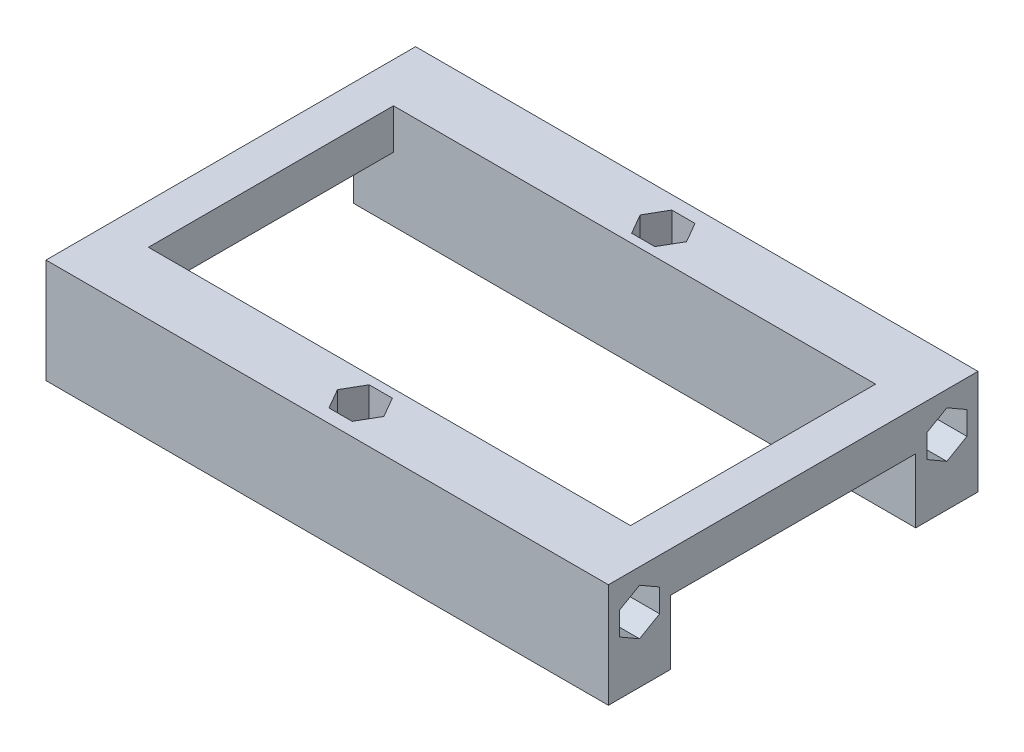
SolidWorks part; units mm, degrees
ref_plane "Front Plane" through (0, 0, 0) normal (0, 0, 1) x (1, 0, 0)
ref_plane "Top Plane" through (0, 0, 0) normal (0, 1, 0) x (1, 0, 0)
ref_plane "Right Plane" through (0, 0, 0) normal (1, 0, 0) x (0, 0, -1)
sketch "Sketch1" plane through (0, 0, 0) normal (0, 1, 0) x (1, 0, 0)
  line L1 (-35, -23) -> (35, -23)
  line L2 (-35, -23) -> (-35, 23)
  line L3 (-35, 23) -> (35, 23)
  line L4 (35, -23) -> (35, 23)
  line L5 (-35, -23) -> (35, 23) construction
  line L6 (-35, 23) -> (35, -23) construction
  point P0 (0, 0)
extrude "Boss-Extrude1" add sketch "Sketch1" along normal blind 5
sketch "Sketch2" plane through (0, 0, 0) normal (0, 1, 0) x (1, 0, 0)
  line L1 (-30, 15.25) -> (30, 15.25)
  line L2 (-30, 15.25) -> (-30, -15.25)
  line L3 (-30, -15.25) -> (30, -15.25)
  line L4 (30, 15.25) -> (30, -15.25)
  line L5 (-30, 15.25) -> (30, -15.25) construction
  line L6 (-30, -15.25) -> (30, 15.25) construction
  point P0 (0, 0)
extrude "Cut-Extrude1" cut sketch "Sketch2" along normal blind 5
sketch "Sketch3" plane through (0, 0, 0) normal (0, 1, 0) x (1, 0, 0)
  line L0 (35, -23) -> (35, 23) construction
  line L1 (-35, -23) -> (35, -23)
  line L2 (-35, -23) -> (-35, -15.25)
  line L3 (-35, -15.25) -> (35, -15.25)
  line L4 (35, -23) -> (35, -15.25)
  line L6 (-35, 23) -> (35, 23)
  line L7 (-35, 23) -> (-35, 15.25)
  line L8 (-35, 15.25) -> (35, 15.25)
  line L9 (35, 23) -> (35, 15.25)
extrude "Boss-Extrude2" add sketch "Sketch3" against normal blind 8
ref_plane "Plane1" through (0, 5, 0) normal (0, 1, 0) x (1, 0, 0)
ref_plane "Plane2" through (-35, 0, 0) normal (-1, 0, 0) x (0, 0, 1)
ref_plane "Plane3" through (35, 0, 0) normal (1, 0, 0) x (0, 0, -1)
sketch "Sketch6" plane through (-35, 0, 0) normal (-1, 0, 0) x (0, 0, 1)
  line L0 (-23, 5) -> (-15.25, -4.75) construction
  line L1 (-15.25, -8) -> (-15.25, 0) construction
  line L2 (23, 5) -> (15.25, -4.75) construction
  line L3 (15.25, -8) -> (15.25, 0) construction
  line L5 (19.125, -2.7618) -> (21.625, -1.3184)
  line L6 (21.625, -1.3184) -> (21.625, 1.5684)
  line L7 (21.625, 1.5684) -> (19.125, 3.0118)
  line L8 (19.125, 3.0118) -> (16.625, 1.5684)
  line L9 (16.625, 1.5684) -> (16.625, -1.3184)
  line L10 (16.625, -1.3184) -> (19.125, -2.7618)
  line L11 (-19.125, -2.7618) -> (-16.625, -1.3184)
  line L12 (-16.625, -1.3184) -> (-16.625, 1.5684)
  line L13 (-16.625, 1.5684) -> (-19.125, 3.0118)
  line L14 (-19.125, 3.0118) -> (-21.625, 1.5684)
  line L15 (-21.625, 1.5684) -> (-21.625, -1.3184)
  line L16 (-21.625, -1.3184) -> (-19.125, -2.7618)
  circle A0 centre (19.125, 0.125) radius 2.5 construction
  circle A1 centre (-19.125, 0.125) radius 2.5 construction
extrude "Cut-Extrude4" cut sketch "Sketch6" against normal blind 8.5
sketch "Sketch7" plane through (35, 0, 0) normal (1, 0, 0) x (0, 0, -1)
  line L0 (23, 5) -> (15.25, -4.75) construction
  line L1 (15.25, -8) -> (15.25, 0) construction
  line L2 (-23, 5) -> (-15.25, -4.75) construction
  line L3 (-15.25, -8) -> (-15.25, 0) construction
  line L5 (-19.125, -2.7618) -> (-16.625, -1.3184)
  line L6 (-16.625, -1.3184) -> (-16.625, 1.5684)
  line L7 (-16.625, 1.5684) -> (-19.125, 3.0118)
  line L8 (-19.125, 3.0118) -> (-21.625, 1.5684)
  line L9 (-21.625, 1.5684) -> (-21.625, -1.3184)
  line L10 (-21.625, -1.3184) -> (-19.125, -2.7618)
  line L11 (19.125, -2.7618) -> (21.625, -1.3184)
  line L12 (21.625, -1.3184) -> (21.625, 1.5684)
  line L13 (21.625, 1.5684) -> (19.125, 3.0118)
  line L14 (19.125, 3.0118) -> (16.625, 1.5684)
  line L15 (16.625, 1.5684) -> (16.625, -1.3184)
  line L16 (16.625, -1.3184) -> (19.125, -2.7618)
  circle A0 centre (-19.125, 0.125) radius 2.5 construction
  circle A1 centre (19.125, 0.125) radius 2.5 construction
  point P19 (0, 0)
  point P27 (0, 0)
extrude "Cut-Extrude5" cut sketch "Sketch7" against normal blind 8.5
sketch "Sketch10" plane through (0, 5, 0) normal (0, 1, 0) x (1, 0, 0)
  line L0 (0, 0) -> (0, -18.835) construction
  line L1 (0, 0) -> (0, 18.835) construction
  line L3 (2.8868, 18.835) -> (1.4434, 21.335)
  line L4 (1.4434, 21.335) -> (-1.4434, 21.335)
  line L5 (-1.4434, 21.335) -> (-2.8868, 18.835)
  line L6 (-2.8868, 18.835) -> (-1.4434, 16.335)
  line L7 (-1.4434, 16.335) -> (1.4434, 16.335)
  line L8 (1.4434, 16.335) -> (2.8868, 18.835)
  line L9 (2.8868, -18.835) -> (1.4434, -16.335)
  line L10 (1.4434, -16.335) -> (-1.4434, -16.335)
  line L11 (-1.4434, -16.335) -> (-2.8868, -18.835)
  line L12 (-2.8868, -18.835) -> (-1.4434, -21.335)
  line L13 (-1.4434, -21.335) -> (1.4434, -21.335)
  line L14 (1.4434, -21.335) -> (2.8868, -18.835)
  circle A0 centre (0, 18.835) radius 2.5 construction
  circle A1 centre (0, -18.835) radius 2.5 construction
extrude "Cut-Extrude6" cut sketch "Sketch10" against normal blind 8.5
